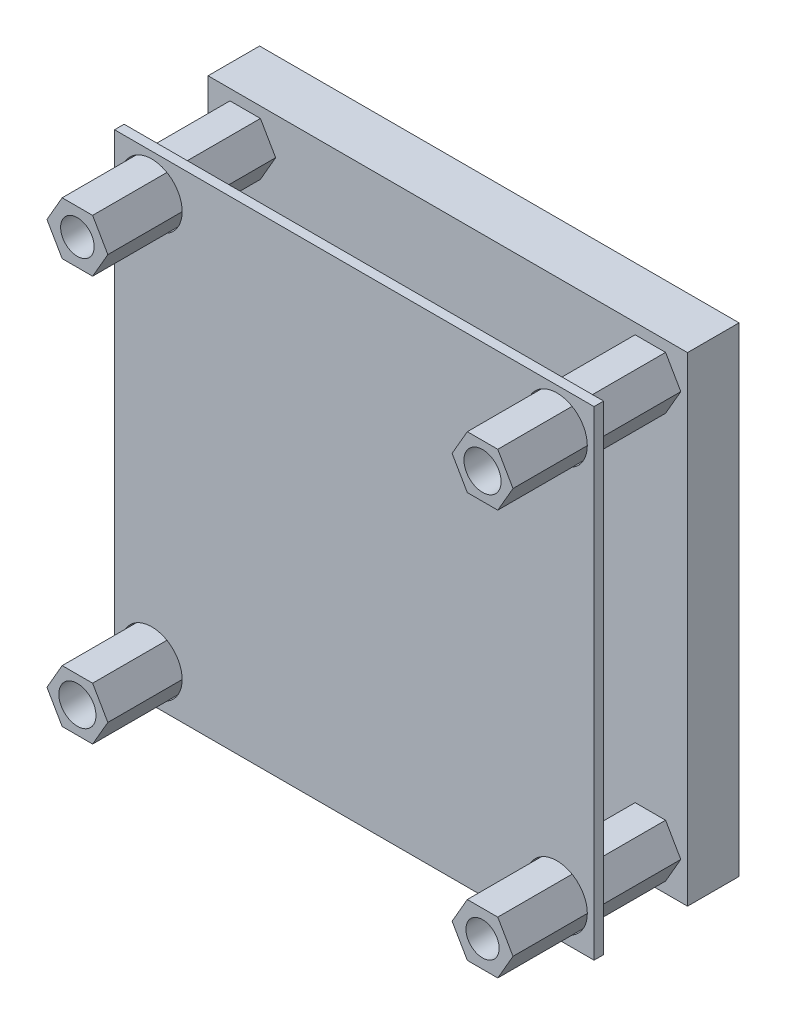
SolidWorks part; units mm, degrees
ref_plane "Front Plane" through (0, 0, 0) normal (0, 0, 1) x (1, 0, 0)
ref_plane "Top Plane" through (0, 0, 0) normal (0, 1, 0) x (1, 0, 0)
ref_plane "Right Plane" through (0, 0, 0) normal (1, 0, 0) x (0, 0, -1)
sketch "Sketch1" plane through (0, 0, 0) normal (0, 0, 1) x (1, 0, 0)
  line L1 (-20, 20) -> (20, 20)
  line L2 (-20, 20) -> (-20, -20)
  line L3 (-20, -20) -> (20, -20)
  line L4 (20, 20) -> (20, -20)
  line L5 (-20, 20) -> (20, -20) construction
  line L6 (-20, -20) -> (20, 20) construction
  point P0 (0, 0)
  dimension "D1" = 40
  dimension "D2" = 40
extrude "Boss-Extrude1" add sketch "Sketch1" along normal blind 4.3
sketch "Sketch2" plane through (0, 0, 4.3) normal (0, 0, 1) x (1, 0, 0)
  line L0 (-20, 20) -> (-20, -20) construction
  line L1 (20, 20) -> (-20, 20) construction
  line L2 (20, -20) -> (20, 20) construction
  line L3 (-20, -20) -> (20, -20) construction
  line L5 (-14.3597, 16.9) -> (-15.6298, 19.1)
  line L6 (-15.6298, 19.1) -> (-18.1702, 19.1)
  line L7 (-18.1702, 19.1) -> (-19.4403, 16.9)
  line L8 (-19.4403, 16.9) -> (-18.1702, 14.7)
  line L9 (-18.1702, 14.7) -> (-15.6298, 14.7)
  line L10 (-15.6298, 14.7) -> (-14.3597, 16.9)
  line L11 (14.3597, 16.9) -> (15.6298, 14.7)
  line L12 (15.6298, 14.7) -> (18.1702, 14.7)
  line L13 (18.1702, 14.7) -> (19.4403, 16.9)
  line L14 (19.4403, 16.9) -> (18.1702, 19.1)
  line L15 (18.1702, 19.1) -> (15.6298, 19.1)
  line L16 (15.6298, 19.1) -> (14.3597, 16.9)
  line L17 (-14.3597, -16.9) -> (-15.6298, -14.7)
  line L18 (-15.6298, -14.7) -> (-18.1702, -14.7)
  line L19 (-18.1702, -14.7) -> (-19.4403, -16.9)
  line L20 (-19.4403, -16.9) -> (-18.1702, -19.1)
  line L21 (-18.1702, -19.1) -> (-15.6298, -19.1)
  line L22 (-15.6298, -19.1) -> (-14.3597, -16.9)
  line L23 (19.4403, -16.9) -> (18.1702, -14.7)
  line L24 (18.1702, -14.7) -> (15.6298, -14.7)
  line L25 (15.6298, -14.7) -> (14.3597, -16.9)
  line L26 (14.3597, -16.9) -> (15.6298, -19.1)
  line L27 (15.6298, -19.1) -> (18.1702, -19.1)
  line L28 (18.1702, -19.1) -> (19.4403, -16.9)
  circle A0 centre (-16.9, 16.9) radius 2.2 construction
  circle A1 centre (-16.9, 16.9) radius 1.4
  circle A2 centre (16.9, 16.9) radius 2.2 construction
  circle A3 centre (-16.9, -16.9) radius 2.2 construction
  circle A4 centre (16.9, -16.9) radius 2.2 construction
  circle A5 centre (-16.9, -16.9) radius 1.55
  circle A6 centre (16.9, -16.9) radius 1.384
  circle A7 centre (16.9, 16.9) radius 1.55
  point P0 (-16.9, 16.9)
  point P1 (16.9, 16.9)
  point P2 (16.9, -16.9)
  point P3 (-16.9, -16.9)
  dimension "D1" = 3.1
  dimension "D2" = 3.1
  dimension "D3" = 3.1
  dimension "D4" = 3.1
extrude "Boss-Extrude2" add sketch "Sketch2" along normal blind 14 separate body
ref_plane "Plane1" through (0, 0, 11.3) normal (0, 0, 1) x (1, 0, 0)
sketch "Sketch4" plane through (0, 0, 11.3) normal (0, 0, 1) x (1, 0, 0)
  line L1 (-20, 20) -> (20, 20)
  line L2 (-20, 20) -> (-20, -20)
  line L3 (-20, -20) -> (20, -20)
  line L4 (20, 20) -> (20, -20)
  line L5 (-20, 20) -> (20, -20) construction
  line L6 (-20, -20) -> (20, 20) construction
  circle A0 centre (-16.9, 16.9) radius 2.5403
  circle A1 centre (16.9, 16.9) radius 2.5403
  circle A2 centre (16.9, -16.9) radius 2.5403
  circle A3 centre (-16.9, -16.9) radius 2.5403
  point P0 (0, 0)
extrude "Boss-Extrude3" add sketch "Sketch4" along normal blind 0.8 separate body
